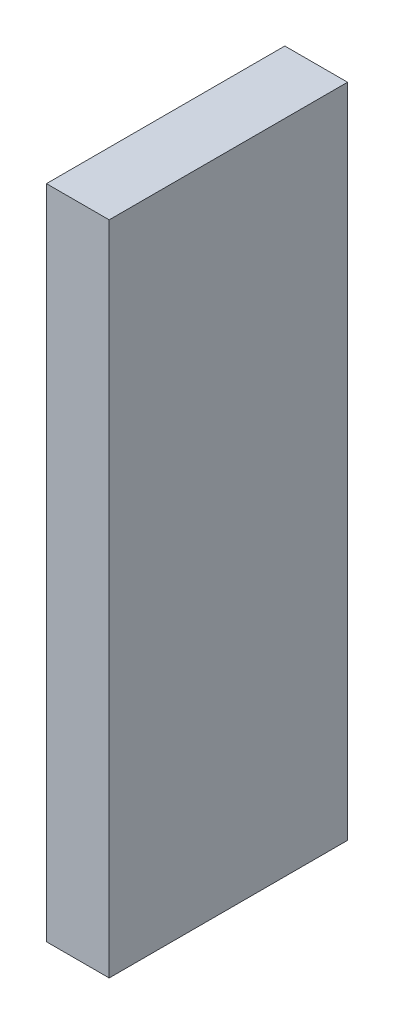
SolidWorks part; units mm, degrees
material "Alloy Steel"
ref_plane "Front Plane" through (0, 0, 0) normal (0, 0, 1) x (1, 0, 0)
ref_plane "Top Plane" through (0, 0, 0) normal (0, 1, 0) x (1, 0, 0)
ref_plane "Right Plane" through (0, 0, 0) normal (1, 0, 0) x (0, 0, -1)
sketch "Sketch1" plane through (0, 0, 0) normal (0, 0, 1) x (1, 0, 0)
  line L1 (0, 0) -> (15, 0)
  line L2 (0, 0) -> (0, 157)
  line L3 (0, 157) -> (15, 157)
  line L4 (15, 0) -> (15, 157)
  dimension "D1" = 157
  dimension "D2" = 15
extrude "Boss-Extrude1" add sketch "Sketch1" along normal blind 57
